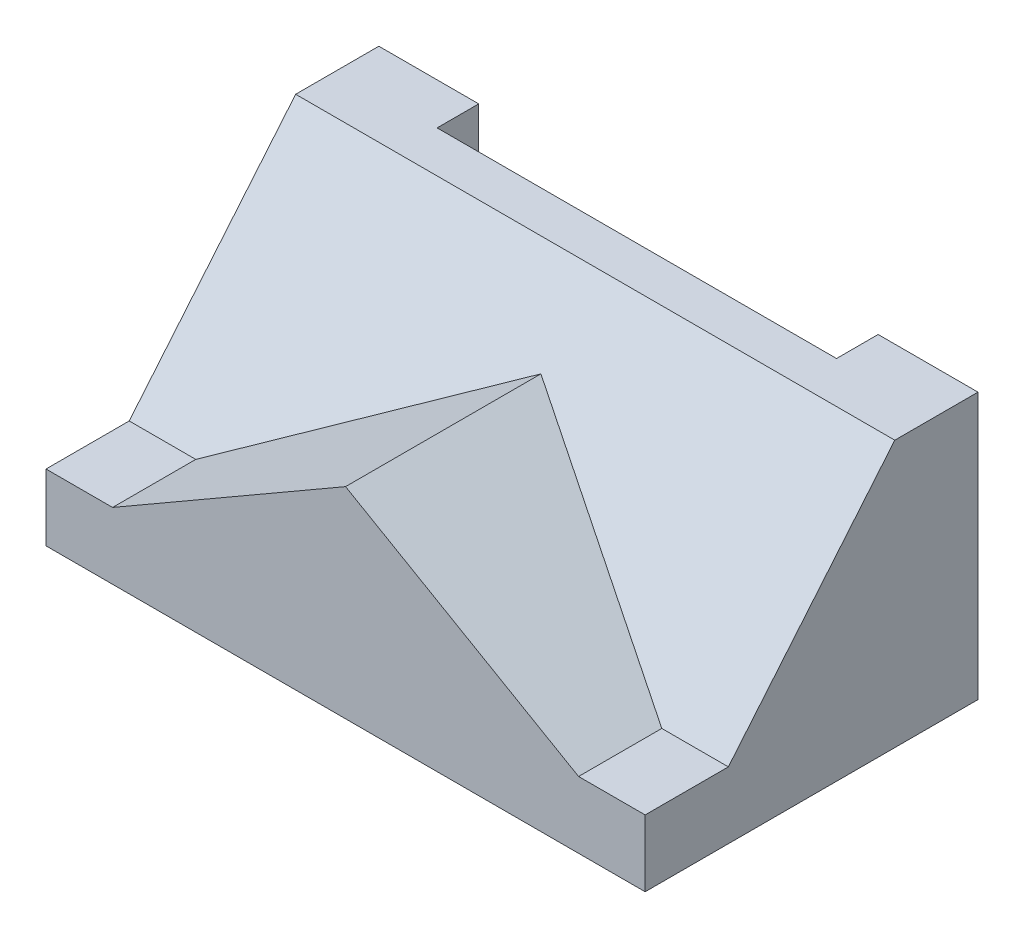
SolidWorks part; units mm, degrees
ref_plane "Front Plane" through (0, 0, 0) normal (0, 0, 1) x (1, 0, 0)
ref_plane "Top Plane" through (0, 0, 0) normal (0, 1, 0) x (1, 0, 0)
ref_plane "Right Plane" through (0, 0, 0) normal (1, 0, 0) x (0, 0, -1)
sketch "Sketch2" plane through (0, 0, 0) normal (1, 0, 0) x (0, 0, -1)
  line L0 (-63.5, 0) -> (0, 0)
  line L1 (0, 0) -> (0, 50.8)
  line L2 (0, 50.8) -> (-15.875, 50.8)
  line L3 (-15.875, 50.8) -> (-47.625, 12.7)
  line L4 (-47.625, 12.7) -> (-63.5, 12.7)
  line L5 (-63.5, 12.7) -> (-63.5, 0)
  dimension "D1" = 50.8
  dimension "D2" = 63.5
  dimension "D3" = 12.7
  dimension "D4" = 15.875
  dimension "D5" = 15.875
extrude "Boss-Extrude1" add sketch "Sketch2" along normal mid plane 114.3
sketch "Sketch3" plane through (0, 0, 63.5) normal (0, 0, 1) x (1, 0, 0)
  line L0 (0, 12.7) -> (0, 34.0697) construction
  line L1 (57.15, 12.7) -> (-57.15, 12.7) construction
  line L2 (-44.45, 12.7) -> (44.45, 12.7)
  line L3 (57.15, 12.7) -> (-57.15, 12.7) construction
  line L4 (44.45, 12.7) -> (0, 38.3632)
  line L5 (-44.45, 12.7) -> (0, 38.3632)
  dimension "D1" = 12.7
  dimension "D2" = 60
extrude "Boss-Extrude2" add sketch "Sketch3" against normal up to next
sketch "Sketch4" plane through (0, 50.8, 0) normal (0, 1, 0) x (1, 0, 0)
  line L0 (57.15, 0) -> (-57.15, 0) construction
  line L1 (-38.1, 0) -> (38.1, 0)
  line L2 (-38.1, 0) -> (-38.1, -7.9375)
  line L3 (-38.1, -7.9375) -> (38.1, -7.9375)
  line L4 (38.1, 0) -> (38.1, -7.9375)
  line L5 (57.15, 0) -> (57.15, -15.875) construction
  point P6 (0, 0)
  point P9 (0, 0)
  dimension "D1" = 19.05
  dimension "D2" = 7.9375
extrude "Cut-Extrude1" cut sketch "Sketch4" against normal up to next
